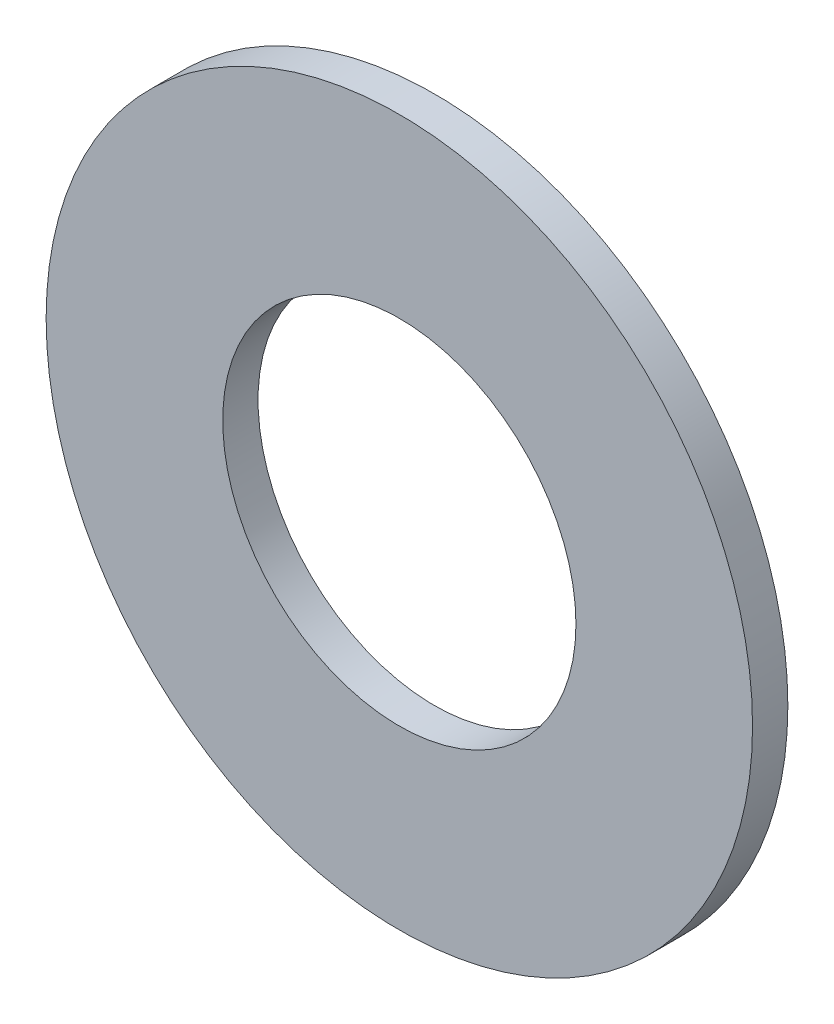
SolidWorks part; units mm, degrees
ref_plane "Front Plane" through (0, 0, 0) normal (0, 0, 1) x (1, 0, 0)
ref_plane "Top Plane" through (0, 0, 0) normal (0, 1, 0) x (1, 0, 0)
ref_plane "Right Plane" through (0, 0, 0) normal (1, 0, 0) x (0, 0, -1)
sketch "Sketch1" plane through (0, 0, 0) normal (0, 0, 1) x (1, 0, 0)
  circle A0 centre (0, 0) radius 5
  circle A1 centre (0, 0) radius 10
  dimension "D1" = 10
  dimension "D2" = 20
extrude "Boss-Extrude1" add sketch "Sketch1" along normal blind 1
